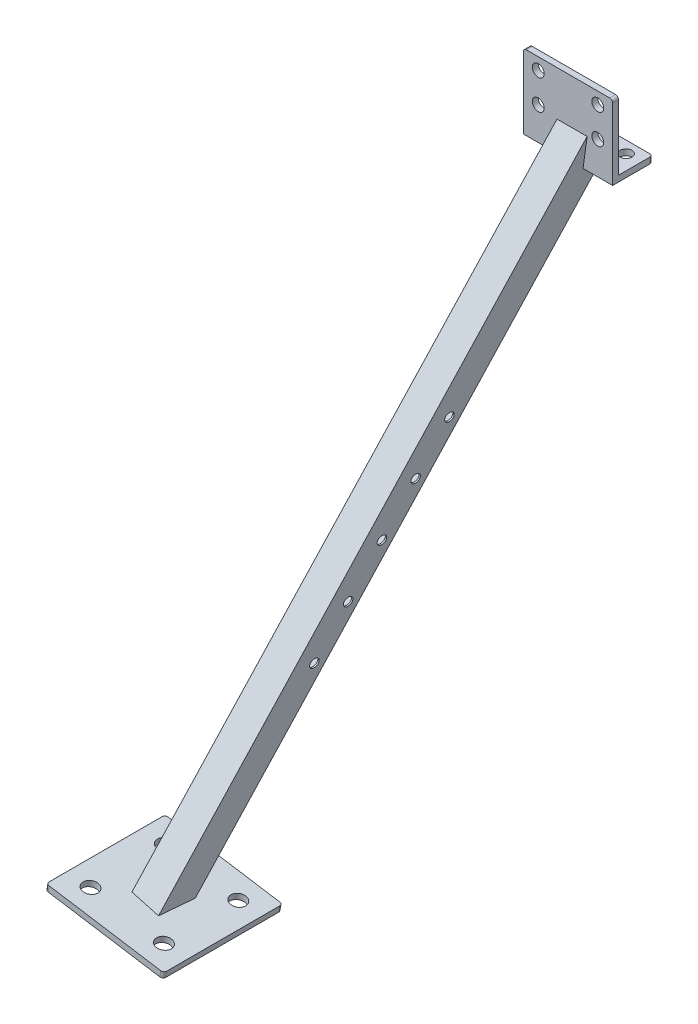
SolidWorks part; units mm, degrees
ref_plane "Front Plane" through (0, 0, 0) normal (0, 0, 1) x (1, 0, 0)
ref_plane "Top Plane" through (0, 0, 0) normal (0, 1, 0) x (1, 0, 0)
ref_plane "Right Plane" through (0, 0, 0) normal (1, 0, 0) x (0, 0, -1)
sketch "Sketch1" plane through (0, 0, 0) normal (1, 0, 0) x (0, 0, -1)
  line L0 (0, 0) -> (0, 50)
  line L1 (0, 50) -> (4, 50)
  line L2 (4, 50) -> (4, 4)
  line L3 (4, 4) -> (27, 4)
  line L4 (27, 4) -> (27, 0)
  line L5 (27, 0) -> (0, 0)
  dimension "D1" = 4
  dimension "D2" = 4
  dimension "D3" = 50
  dimension "D4" = 27
extrude "Boss-Extrude1" add sketch "Sketch1" along normal blind 60
ref_plane "Plane1" through (0, 0, 0) normal (0, -0.866, 0.5) x (-1, 0, 0)
sketch "Sketch2" plane through (0, 0, 0) normal (0, -0.866, 0.5) x (-1, 0, 0)
  line L0 (-30, 0) -> (-30, 23.3827)
  line L1 (-60, 0) -> (0, 0) construction
  line L2 (-60, 23.3827) -> (0, 23.3827) construction
ref_plane "Plane2" through (0.7342, 4.0142, -2.3176) normal (-0.1564, -0.8554, 0.4938) x (0, -0.5, -0.866)
sketch "Sketch3" plane through (0.7342, 4.0142, -2.3176) normal (-0.1564, -0.8554, 0.4938) x (0, -0.5, -0.866)
  line L0 (-9, 38.6307) -> (9, 38.6307)
  line L1 (-10, 39.6307) -> (10, 39.6307)
  line L2 (-10, 39.6307) -> (-10, 19.6307)
  line L3 (-10, 19.6307) -> (10, 19.6307)
  line L4 (10, 39.6307) -> (10, 19.6307)
  line L5 (-10, 39.6307) -> (10, 19.6307) construction
  line L6 (-10, 19.6307) -> (10, 39.6307) construction
  line L7 (9, 38.6307) -> (9, 20.6307)
  line L8 (-9, 20.6307) -> (9, 20.6307)
  line L9 (-9, 38.6307) -> (-9, 20.6307)
  point P0 (0, 29.6307)
  dimension "D1" = 20
  dimension "D2" = 20
  dimension "D3" = 1
extrude "Boss-Extrude2" add sketch "Sketch3" along normal blind 500 and the other way blind 20
sketch "Sketch4" plane through (0, 0, 0) normal (-1, 0, 0) x (0, 0, 1)
  line L0 (-4, 4) -> (-4, 34.4259)
  line L1 (-4, 4) -> (-4, 50) construction
  line L2 (-4, 34.4259) -> (-31.384, 4)
  line L3 (-27, 4) -> (-4, 4) construction
  line L4 (-31.384, 4) -> (-4, 4)
extrude "Cut-Extrude1" cut sketch "Sketch4" against normal blind 60
ref_plane "Plane3" through (-56.757, -358.3494, 0) normal (0.1564, 0.9877, 0) x (0.9877, -0.1564, 0)
sketch "Sketch6" plane through (-56.757, -358.3494, 0) normal (0.1564, 0.9877, 0) x (0.9877, -0.1564, 0)
  line L0 (28.4656, -256.3645) -> (8.5312, -254.8002) construction
  line L2 (19.2115, 0) -> (8.5312, -254.8002) construction
  line L4 (60.6025, -165.5937) -> (-19.3975, -165.5937)
  line L5 (60.6025, -165.5937) -> (60.6025, -245.5937)
  line L6 (60.6025, -245.5937) -> (-19.3975, -245.5937)
  line L7 (-19.3975, -165.5937) -> (-19.3975, -245.5937)
  line L8 (60.6025, -165.5937) -> (-19.3975, -245.5937) construction
  line L9 (60.6025, -245.5937) -> (-19.3975, -165.5937) construction
  point P0 (20.6025, -205.5937)
  point P6 (20.6025, -205.5937)
  dimension "D1" = 50
  dimension "D2" = 10
  dimension "D3" = 80
  dimension "D4" = 80
extrude "Boss-Extrude3" add sketch "Sketch6" along normal blind 4
sketch "Sketch7" plane through (-56.757, -358.3494, 0) normal (-0.1564, -0.9877, 0) x (0.9877, -0.1564, 0)
  line L1 (-14.2325, 168.7738) -> (52.3005, 168.7738)
  line L2 (-14.2325, 168.7738) -> (-14.2325, 268.7738)
  line L3 (-14.2325, 268.7738) -> (52.3005, 268.7738)
  line L4 (52.3005, 168.7738) -> (52.3005, 268.7738)
  line L5 (-14.2325, 168.7738) -> (52.3005, 268.7738) construction
  line L6 (-14.2325, 268.7738) -> (52.3005, 168.7738) construction
  point P0 (19.034, 218.7738)
  dimension "D1" = 100
extrude "Cut-Extrude2" cut sketch "Sketch7" along normal blind 100
sketch "Sketch8" plane through (0, 0, 0) normal (0, 0, 1) x (1, 0, 0)
  circle A0 centre (10, 22) radius 4 construction
  circle A1 centre (50, 22) radius 4 construction
  circle A2 centre (50, 42) radius 4 construction
  circle A3 centre (10, 42) radius 4 construction
  circle A4 centre (10, 22) radius 4
  circle A5 centre (50, 22) radius 4
  circle A6 centre (50, 42) radius 4
  circle A7 centre (10, 42) radius 4
extrude "Cut-Extrude3" cut sketch "Sketch8" against normal up to next
sketch "Sketch9" plane through (0, 0, 0) normal (0, -1, 0) x (1, 0, 0)
  circle A0 centre (50, -19) radius 4 construction
  circle A1 centre (10, -19) radius 4 construction
  circle A2 centre (50, -19) radius 4
  circle A3 centre (10, -19) radius 4
extrude "Cut-Extrude4" cut sketch "Sketch9" against normal up to next
sketch "Sketch10" plane through (-56.757, -358.3494, 0) normal (-0.1564, -0.9877, 0) x (0.9877, -0.1564, 0)
  line L0 (-19.3975, 245.5937) -> (60.6025, 245.5937) construction
  line L1 (-19.3975, 165.5937) -> (-19.3975, 245.5937) construction
  circle A0 centre (-4.3975, 230.5937) radius 5
  circle A1 centre (45.6025, 230.5937) radius 5
  circle A2 centre (45.6025, 180.5937) radius 5
  circle A3 centre (-4.3975, 180.5937) radius 5
  dimension "D1" = 10
  dimension "D2" = 15
  dimension "D3" = 15
  dimension "D4" = 2
  dimension "D5" = 2
extrude "Cut-Extrude5" cut sketch "Sketch10" against normal up to next
fillet "Fillet1" radius 2 4 edges at (-75.6028, -353.3396, 245.5937) (-75.6028, -353.3396, 165.5937) (3.4123, -365.8544, 165.5937) (3.4123, -365.8544, 245.5937)
fillet "Fillet2" radius 2 4 edges at (60, 2, -27) (0, 2, -27) (60, 50, -2) (0, 50, -2)
sketch "Sketch11" plane through (19.389, -2.6595, 1.5355) normal (-0.9877, 0.1355, -0.0782) x (-0.0775, 0.0106, 0.9969)
  ellipse E0 centre (133.9733, -240.0897) end of major axis (134.7432, -242.9892) minor radius 2.9902 construction
  ellipse E1 centre (116.6926, -209.6618) end of major axis (117.4625, -212.5613) minor radius 2.9902 construction
  ellipse E2 centre (99.4119, -179.2339) end of major axis (100.1817, -182.1335) minor radius 2.9902 construction
  ellipse E3 centre (82.1311, -148.8061) end of major axis (82.901, -151.7056) minor radius 2.9902 construction
  ellipse E4 centre (64.8504, -118.3782) end of major axis (65.6203, -121.2777) minor radius 2.9902 construction
  ellipse E5 centre (133.9733, -240.0897) end of major axis (134.7432, -242.9892) minor radius 2.9902
  ellipse E6 centre (116.6926, -209.6618) end of major axis (117.4625, -212.5613) minor radius 2.9902
  ellipse E7 centre (99.4119, -179.2339) end of major axis (100.1817, -182.1335) minor radius 2.9902
  ellipse E8 centre (82.1311, -148.8061) end of major axis (82.901, -151.7056) minor radius 2.9902
  ellipse E9 centre (64.8504, -118.3782) end of major axis (65.6203, -121.2777) minor radius 2.9902
extrude "Cut-Extrude6" cut sketch "Sketch11" against normal through all
